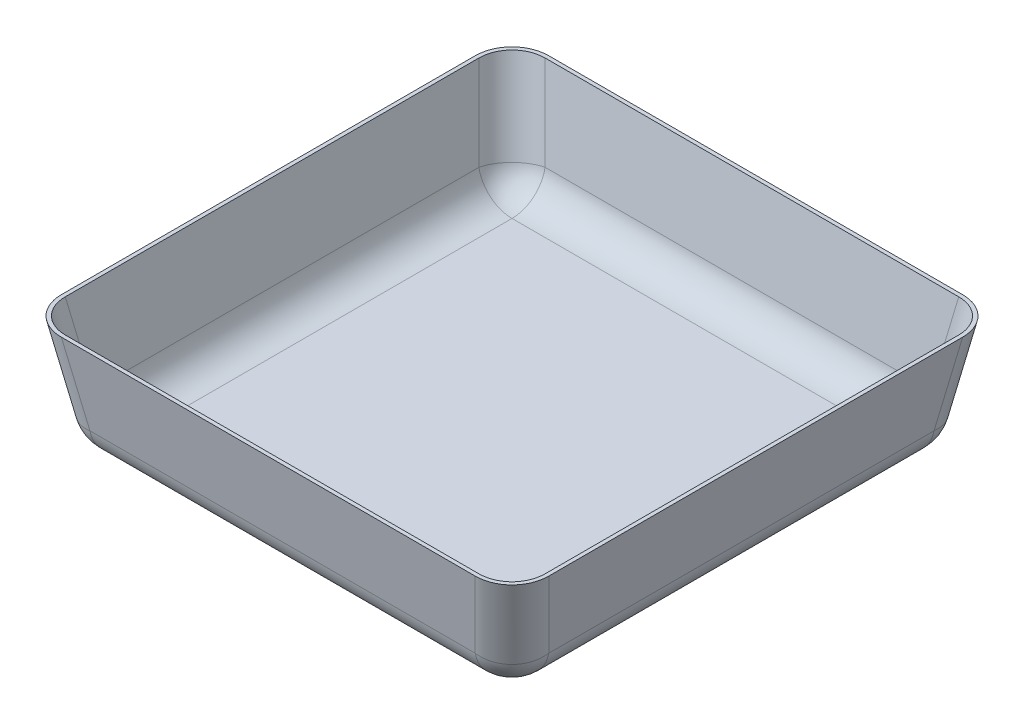
SolidWorks part; units mm, degrees
ref_plane "Front Plane" through (0, 0, 0) normal (0, 0, 1) x (1, 0, 0)
ref_plane "Top Plane" through (0, 0, 0) normal (0, 1, 0) x (1, 0, 0)
ref_plane "Right Plane" through (0, 0, 0) normal (1, 0, 0) x (0, 0, -1)
sketch "Sketch1" plane through (0, 0, 0) normal (0, 1, 0) x (1, 0, 0)
  line L1 (-152.4, 152.4) -> (152.4, 152.4)
  line L2 (-152.4, 152.4) -> (-152.4, -152.4)
  line L3 (-152.4, -152.4) -> (152.4, -152.4)
  line L4 (152.4, 152.4) -> (152.4, -152.4)
  line L5 (-152.4, 152.4) -> (152.4, -152.4) construction
  line L6 (-152.4, -152.4) -> (152.4, 152.4) construction
  point P0 (0, 0)
  dimension "D1" = 304.8
extrude "Boss-Extrude1" add sketch "Sketch1" along normal blind 76.2 draft 10 draft outward yes
fillet "Fillet2" radius 25.4 8 edges at (0, 0, -152.4) (-152.4, 0, 0) (0, 0, 152.4) (152.4, 0, 0) (-159.1181, 38.1, 159.1181) (-159.1181, 38.1, -159.1181) (159.1181, 38.1, 159.1181) (159.1181, 38.1, -159.1181)
shell "Shell1" thickness 2.54
